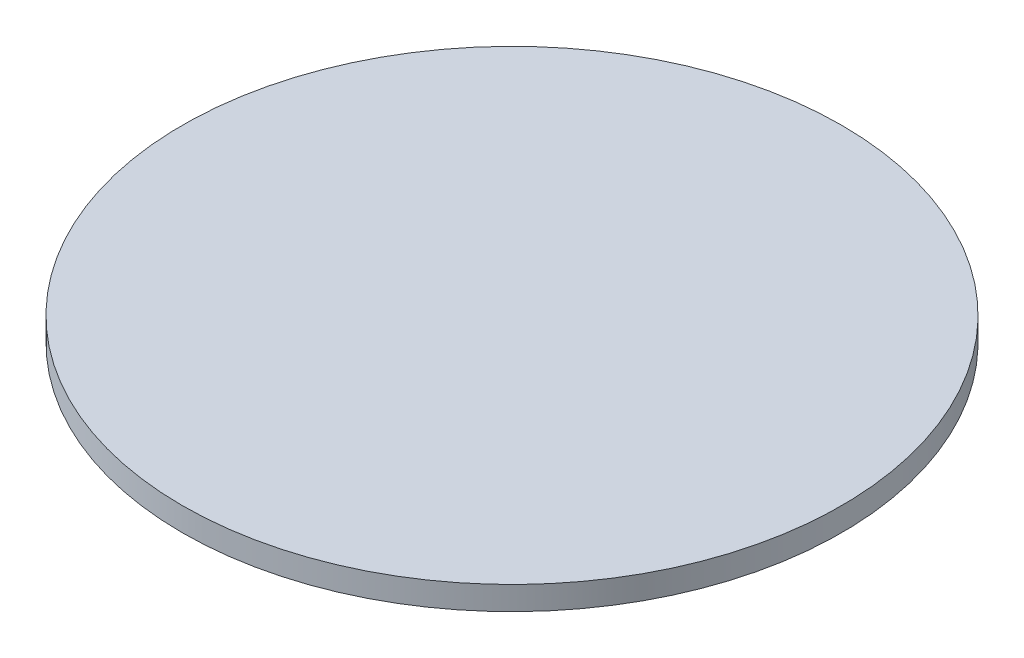
SolidWorks part; units mm, degrees
material "AISI 304"
ref_plane "Front Plane" through (0, 0, 0) normal (0, 0, 1) x (1, 0, 0)
ref_plane "Top Plane" through (0, 0, 0) normal (0, 1, 0) x (1, 0, 0)
ref_plane "Right Plane" through (0, 0, 0) normal (1, 0, 0) x (0, 0, -1)
sketch "Sketch1" plane through (0, 0, 0) normal (0, 1, 0) x (1, 0, 0)
  circle A0 centre (0, 0) radius 177.8
extrude "Boss-Extrude1" add sketch "Sketch1" along normal mid plane 12.7
